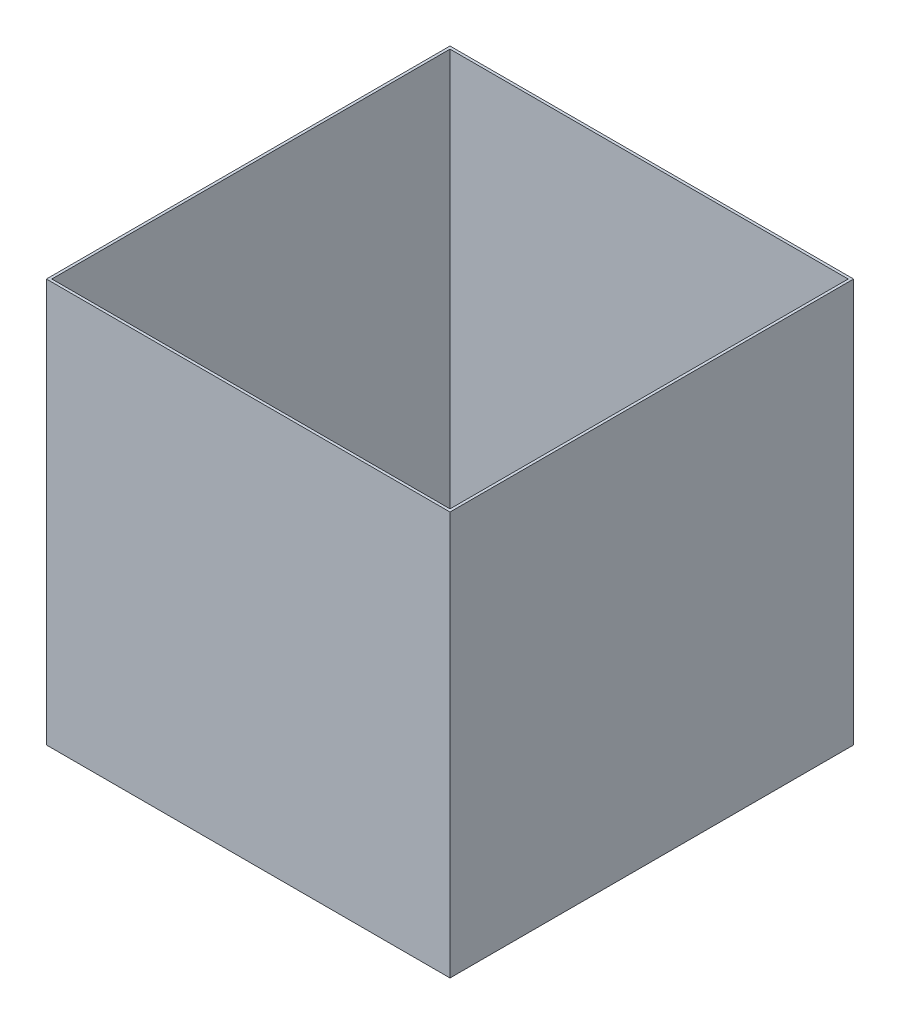
SolidWorks part; units mm, degrees
material "Acrylic (Medium-high impact)"
ref_plane "Front Plane" through (0, 0, 0) normal (0, 0, 1) x (1, 0, 0)
ref_plane "Top Plane" through (0, 0, 0) normal (0, 1, 0) x (1, 0, 0)
ref_plane "Right Plane" through (0, 0, 0) normal (1, 0, 0) x (0, 0, -1)
sketch "Sketch1" plane through (0, 0, 0) normal (0, 1, 0) x (1, 0, 0)
  line L1 (-150, 150) -> (150, 150)
  line L2 (-150, 150) -> (-150, -150)
  line L3 (-150, -150) -> (150, -150)
  line L4 (150, 150) -> (150, -150)
  line L5 (-150, 150) -> (150, -150) construction
  line L6 (-150, -150) -> (150, 150) construction
  point P0 (0, 0)
  dimension "D1" = 300
extrude "Boss-Extrude1" add sketch "Sketch1" along normal blind 300
shell "Shell1" thickness 2
